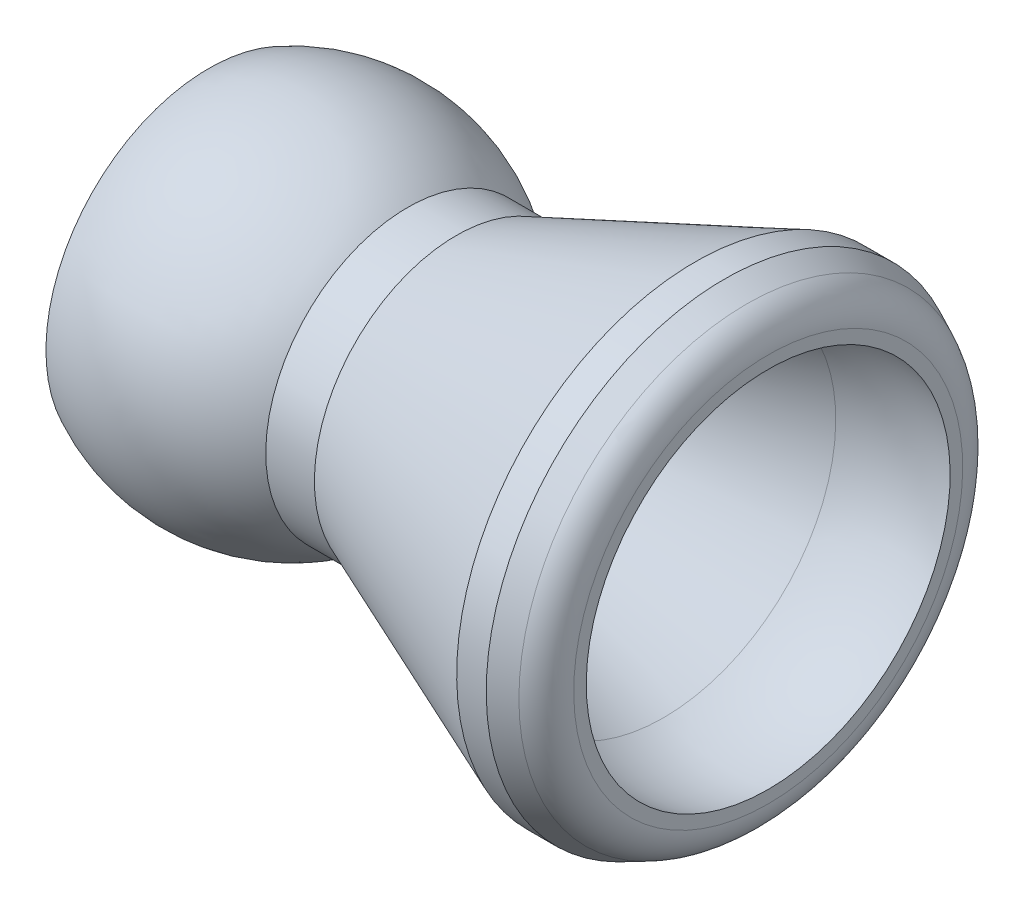
SolidWorks part; units mm, degrees
ref_plane "Front Plane" through (0, 0, 0) normal (0, 0, 1) x (1, 0, 0)
ref_plane "Top Plane" through (0, 0, 0) normal (0, 1, 0) x (1, 0, 0)
ref_plane "Right Plane" through (0, 0, 0) normal (1, 0, 0) x (0, 0, -1)
sketch "Sketch1" plane through (0, 0, 0) normal (0, 0, 1) x (1, 0, 0)
  line L0 (-9.6139, 0) -> (9.6139, 0) construction
  line L1 (-9.6139, 5.5931) -> (-9.6139, -5.5931) construction
  line L2 (-2.7762, 4.8768) -> (-2.7762, -4.8768) construction
  line L3 (-2.7762, 4.8768) -> (-1.1049, 4.8768) construction
  line L4 (8.1153, 8.1915) -> (8.1153, -8.1915) construction
  line L5 (-9.6139, 4.5085) -> (-9.6139, -4.5085) construction
  line L6 (0, 3.175) -> (0, -3.175) construction
  line L7 (-152.4, 0) -> (152.4, 0) construction
  arc A0 (-9.6139, 5.5931) -> (-2.7762, 4.8768) centre (-6.7434, 0.0002) cw construction
  point P4 (0, 0)
  point P10 (-9.6139, 0)
  point P13 (-2.7762, 0)
  point P17 (8.1153, 0)
  point P20 (-9.6139, 0)
  point P21 (-1.9406, 4.8768)
  point P24 (0, 0)
  point P27 (0, 0)
  dimension "Male Radius" = 6.2865
  dimension "Overall Length" = 304.8
  dimension "Length" = 19.2278
  dimension "Male Outer Diameter" = 11.1862
  dimension "Male End Length" = 6.8377
  dimension "Neck Diameter" = 9.7536
  dimension "Neck Length" = 1.6713
  dimension "Chamfer Length" = 1.4986
  dimension "Female Outer Diameter" = 16.383
  dimension "Male Inner Diameter" = 9.017
  dimension "Trade Size" = 6.35
sketch "Sketch2" plane through (0, 0, 0) normal (0, 0, 1) x (1, 0, 0)
  line L0 (-9.6139, 5.5931) -> (-9.6139, 4.5085)
  line L1 (-2.7762, 4.8768) -> (-1.1049, 4.8768) construction
  line L2 (-2.7762, 4.8768) -> (-1.1049, 4.8768)
  line L3 (-1.1049, 4.8768) -> (7.0993, 8.1915)
  line L4 (7.0993, 8.1915) -> (8.1153, 8.1915)
  line L5 (8.1153, 8.1915) -> (9.6139, 7.4927)
  line L6 (9.6139, 7.4927) -> (9.6139, 6.2525)
  line L7 (6.0167, 5.9187) -> (-0.7741, 3.175)
  line L8 (2.6213, 4.5468) -> (1.9838, 6.1247) construction
  line L9 (-0.7741, 3.175) -> (-3.1731, 3.175)
  line L10 (-1.9406, 4.8768) -> (-1.9406, 3.175) construction
  line L11 (-3.1731, 3.175) -> (-5.4828, 4.5085)
  line L12 (-9.6139, 4.5085) -> (-5.4828, 4.5085)
  arc A0 (-2.7762, 4.8768) -> (-9.6139, 5.5931) centre (-6.7434, 0.0002) ccw construction
  arc A1 (-2.7762, 4.8768) -> (-9.6139, 5.5931) centre (-6.7434, 0.0002) ccw
  arc A2 (9.6139, 6.2525) -> (6.0167, 5.9187) centre (8.3717, 0.0899) ccw
  point P10 (-6.0885, 6.2525)
  point P17 (9.6139, 6.2525)
  dimension "D1" = 158
  dimension "D2" = 155
  dimension "D3" = 150
  dimension "D4" = 0.3969
revolve "Revolve1" add sketch "Sketch2" angle 360 about L7
fillet "Fillet1" radius 1.27 1 edges at (9.6139, -7.4927, 0)
chamfer "Chamfer1" distance 0.4394 angle 22 1 edges at (-9.6139, -4.5085, 0)
